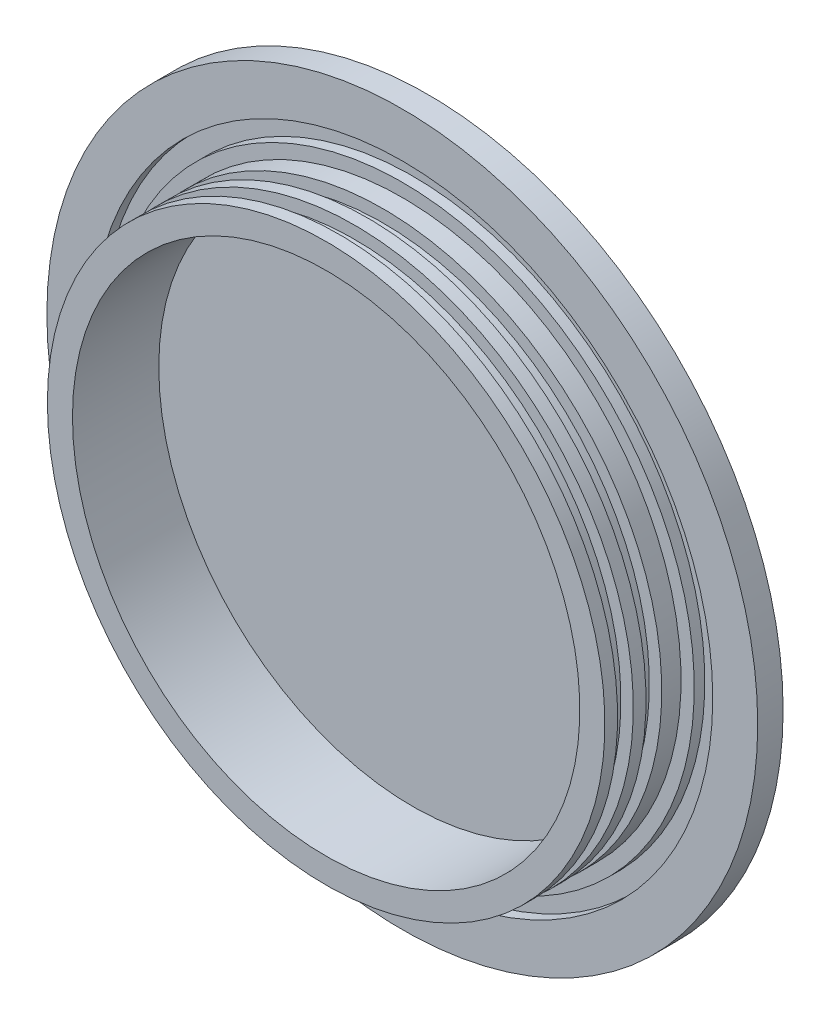
SolidWorks part; units mm, degrees
material "6061-T6 (SS)"
ref_plane "Front Plane" through (0, 0, 0) normal (0, 0, 1) x (1, 0, 0)
ref_plane "Top Plane" through (0, 0, 0) normal (0, 1, 0) x (1, 0, 0)
ref_plane "Right Plane" through (0, 0, 0) normal (1, 0, 0) x (0, 0, -1)
sketch "Sketch1" plane through (0, 0, 0) normal (0, 1, 0) x (1, 0, 0)
  line L0 (0, 0) -> (0, -25.4) construction
  line L1 (0, 0) -> (88.9, 0)
  line L2 (63.4492, -25.4) -> (69.723, -25.4)
  line L3 (69.723, -25.4) -> (69.723, -22.225)
  line L4 (63.4492, -25.4) -> (63.4492, -3.81)
  line L5 (63.4492, -3.81) -> (0, -3.81)
  line L6 (0, -3.81) -> (0, 0)
  line L7 (88.9, 0) -> (88.9, -6.35)
  line L8 (73.025, -3.7084) -> (77.6478, -3.7084)
  line L9 (73.025, -3.7084) -> (73.025, -6.35)
  line L10 (73.025, -6.35) -> (69.723, -6.35)
  line L11 (77.6478, -3.7084) -> (77.6478, -6.35)
  line L12 (77.6478, -6.35) -> (88.9, -6.35)
  line L13 (69.723, -22.225) -> (66.6242, -22.225)
  line L14 (66.6242, -22.225) -> (66.6242, -18.288)
  line L15 (66.6242, -18.288) -> (69.723, -18.288)
  line L16 (69.723, -15.113) -> (66.6242, -15.113)
  line L17 (66.6242, -15.113) -> (66.6242, -11.176)
  line L18 (66.6242, -11.176) -> (69.723, -11.176)
  line L19 (69.723, -11.176) -> (69.723, -6.35)
  line L20 (69.723, -18.288) -> (69.723, -15.113)
  dimension "D1" = 139.446
  dimension "D2" = 6.35
  dimension "D3" = 177.8
  dimension "D4" = 146.05
  dimension "D5" = 3.175
  dimension "D6" = 19.05
  dimension "D7" = 4.6228
  dimension "D8" = 2.6416
  dimension "D9" = 3.0988
  dimension "D10" = 3.937
  dimension "D11" = 3.175
  dimension "D12" = 3.175
  dimension "D13" = 3.81
revolve "Revolve1" add sketch "Sketch1" angle 360 about L0
